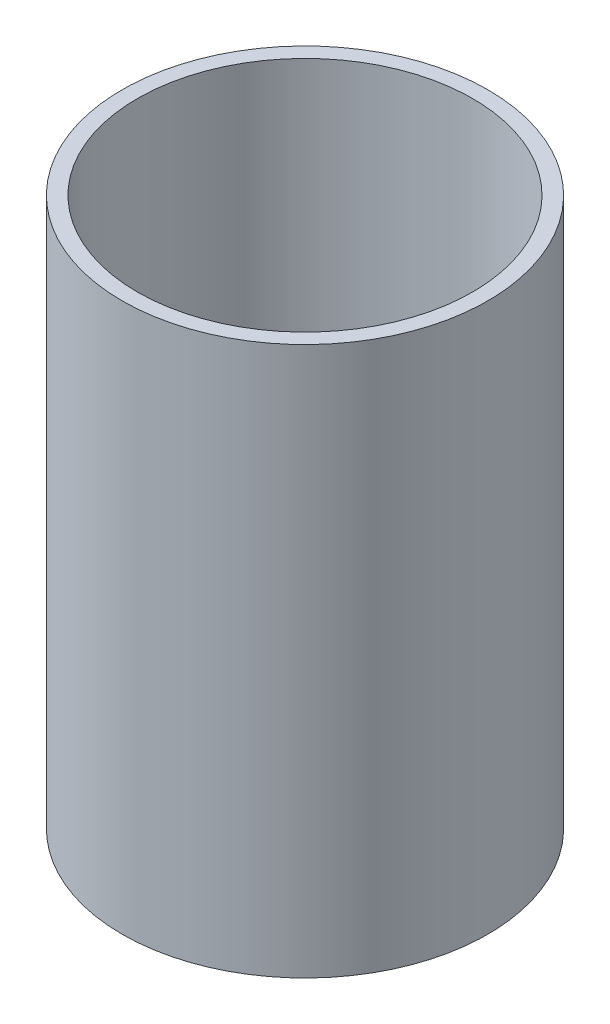
SolidWorks part; units mm, degrees
ref_plane "Front Plane" through (0, 0, 0) normal (0, 0, 1) x (1, 0, 0)
ref_plane "Top Plane" through (0, 0, 0) normal (0, 1, 0) x (1, 0, 0)
ref_plane "Right Plane" through (0, 0, 0) normal (1, 0, 0) x (0, 0, -1)
sketch "Sketch1" plane through (0, 0, 0) normal (0, 1, 0) x (1, 0, 0)
  circle A0 centre (0, 0) radius 304.8
extrude "Boss-Extrude1" add sketch "Sketch1" along normal blind 914.4
sketch "Sketch2" plane through (0, 914.4, 0) normal (0, 1, 0) x (1, 0, 0)
  circle A0 centre (0, 0) radius 279.4
  circle A1 centre (0, 0) radius 304.8
  circle A2 centre (0, 0) radius 304.8
  dimension "D1" = 0
  dimension "D2" = 25.4
extrude "Cut-Extrude2" cut sketch "Sketch2" against normal blind 889 flip side to cut contours A2 | A0
sketch "Sketch3" plane through (0, 0, 0) normal (0, -1, 0) x (1, 0, 0)
  circle A0 centre (0, 0) radius 12.7
extrude "Cut-Extrude3" cut sketch "Sketch3" against normal blind 25.4
